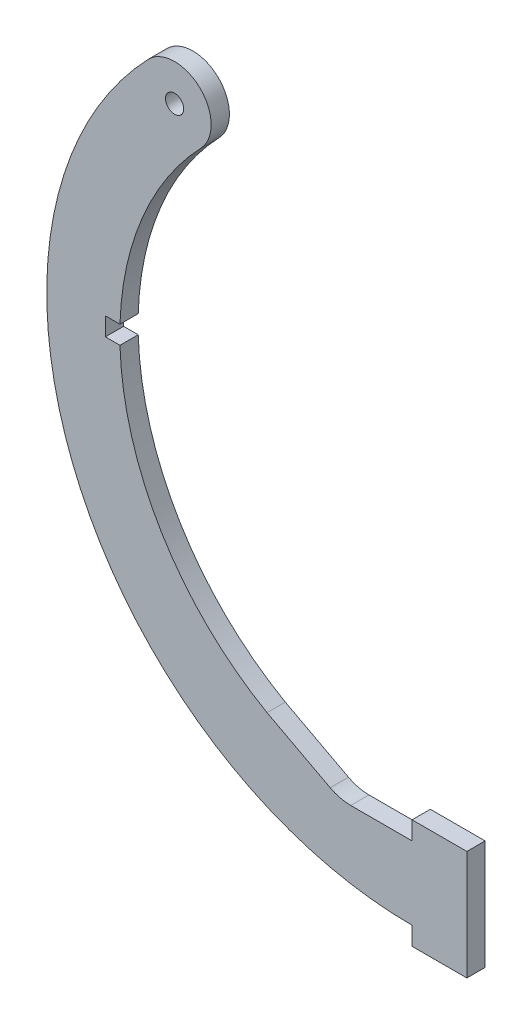
SolidWorks part; units mm, degrees
material "ABS"
ref_plane "Front Plane" through (0, 0, 0) normal (0, 0, 1) x (1, 0, 0)
ref_plane "Top Plane" through (0, 0, 0) normal (0, 1, 0) x (1, 0, 0)
ref_plane "Right Plane" through (0, 0, 0) normal (1, 0, 0) x (0, 0, -1)
sketch "Sketch1" plane through (0, 0, 0) normal (0, 0, 1) x (1, 0, 0)
  line L0 (155.4687, -24.8524) -> (155.4687, 34.419) construction
  line L1 (145.9437, -28.0274) -> (145.9437, -24.8524)
  line L2 (155.4687, -28.0274) -> (155.4687, -40.7274)
  line L3 (145.9437, -28.0274) -> (135.2757, -28.0274)
  line L4 (155.4687, -24.8524) -> (155.4687, -28.0274)
  line L5 (131.7102, -27.1419) -> (120.7292, -21.3281)
  line L6 (145.9437, -40.7274) -> (145.9437, -43.9024)
  line L7 (145.9437, -43.9024) -> (155.4687, -43.9024)
  line L8 (152.2937, -24.8524) -> (155.4687, -24.8524)
  line L9 (145.9437, -24.8524) -> (152.2937, -24.8524)
  line L10 (155.4687, -43.9024) -> (155.4687, -40.7274)
  line L11 (95.1685, 24.3601) -> (92.6285, 24.3601)
  line L12 (92.6285, 24.3601) -> (92.6285, 21.1851)
  line L13 (92.6285, 21.1851) -> (95.1685, 21.1851)
  line L14 (155.4687, 34.419) -> (123.7397, 34.419) construction
  arc A0 (109.2548, 57.9089) -> (95.1685, 24.3601) centre (145.9437, 22.7726) ccw
  arc A1 (100.0825, 66.693) -> (145.9437, -40.7274) centre (145.9437, 22.7726) ccw
  arc A2 (109.2548, 57.9089) -> (100.0825, 66.693) centre (104.6687, 62.301) ccw
  circle A3 centre (104.6687, 62.301) radius 1.5875
  arc A4 (95.5011, 16.7568) -> (120.7292, -21.3281) centre (145.9437, 22.7726) ccw
  arc A5 (95.1685, 21.1851) -> (95.5011, 16.7568) centre (145.9437, 22.7726) ccw
  arc A6 (135.2757, -28.0274) -> (131.7102, -27.1419) centre (135.2757, -20.4074) cw
  point P24 (95.243, 19.5976)
  dimension "D1" = 50.8
  dimension "D2" = 127
  dimension "D3" = 50.8
  dimension "D6" = 7.62
  dimension "D8" = 3.175
  dimension "D4" = 2.54
  dimension "D5" = 3.175
  dimension "D7" = 3.175
  dimension "D9" = 10.668
  dimension "D10" = 9.525
extrude "Boss-Extrude1" add sketch "Sketch1" along normal blind 3.175
